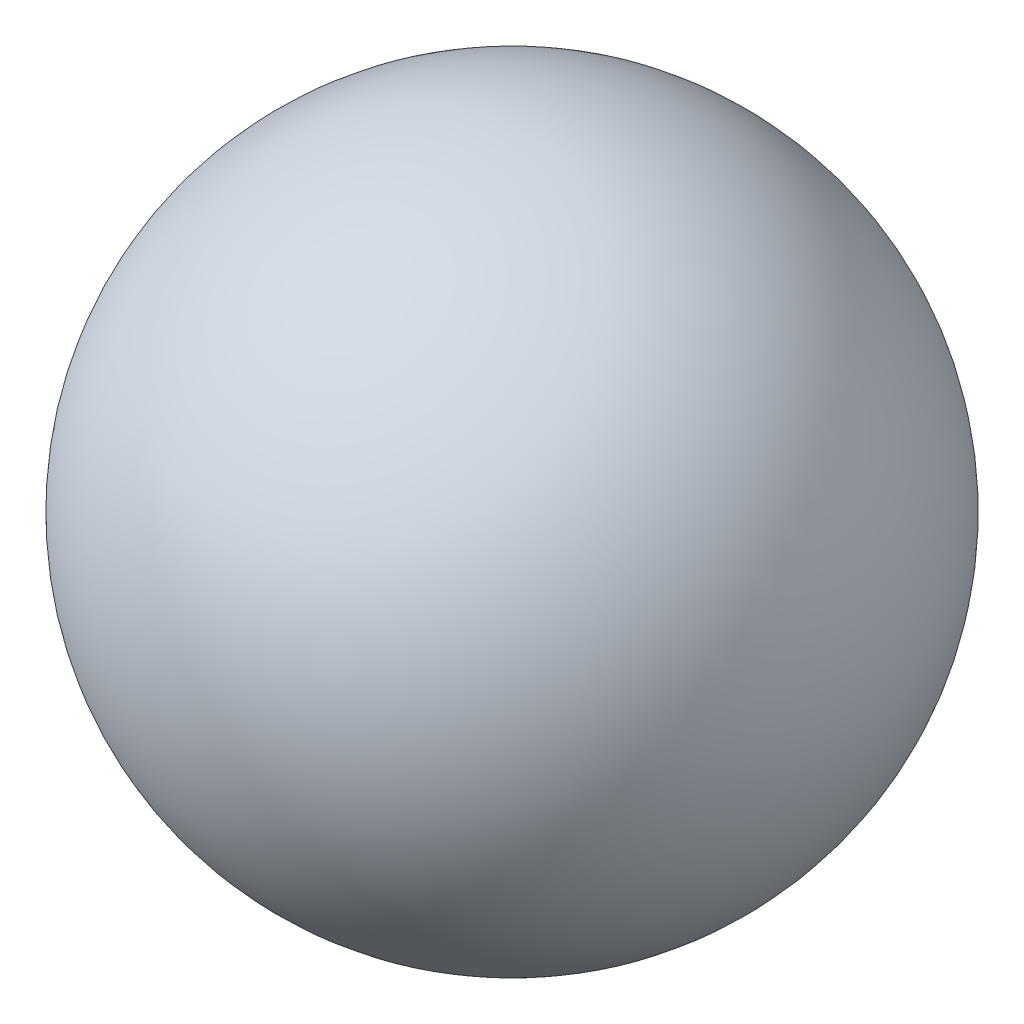
SolidWorks part; units mm, degrees
ref_plane "Front Plane" through (0, 0, 0) normal (0, 0, 1) x (1, 0, 0)
ref_plane "Top Plane" through (0, 0, 0) normal (0, 1, 0) x (1, 0, 0)
ref_plane "Right Plane" through (0, 0, 0) normal (1, 0, 0) x (0, 0, -1)
sketch "Sketch1" plane through (0, 0, 0) normal (1, 0, 0) x (0, 0, -1)
  line L0 (0, 0) -> (0, -165.1) construction
  line L1 (0, 0) -> (0, 165.1) construction
  line L2 (0, -165.1) -> (0, 165.1)
  arc A0 (0, 165.1) -> (0, -165.1) centre (0, 0) cw
  dimension "D1" = 165.1
revolve "Revolve1" add sketch "Sketch1" angle 360 about L2
